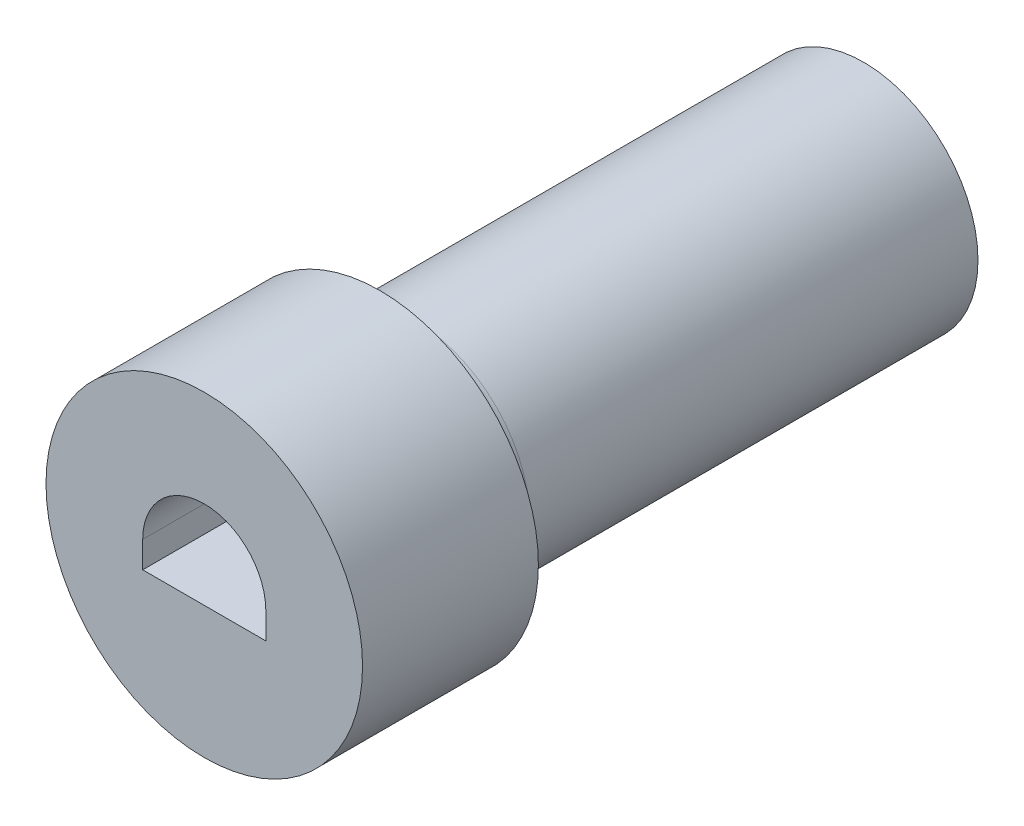
SolidWorks part; units mm, degrees
ref_plane "Front Plane" through (0, 0, 0) normal (0, 0, 1) x (1, 0, 0)
ref_plane "Top Plane" through (0, 0, 0) normal (0, 1, 0) x (1, 0, 0)
ref_plane "Right Plane" through (0, 0, 0) normal (1, 0, 0) x (0, 0, -1)
sketch "Sketch1" plane through (0, 0, 0) normal (0, 0, 1) x (1, 0, 0)
  circle A0 centre (0, 0) radius 1.651
  dimension "D1" = 3.302
extrude "Boss-Extrude1" add sketch "Sketch1" along normal blind 6.985
sketch "Sketch2" plane through (0, 0, 6.985) normal (0, 0, 1) x (1, 0, 0)
  line L0 (-0.889, 0) -> (-0.889, -0.381)
  line L1 (-0.889, -0.381) -> (0.7112, -0.381)
  line L3 (0.889, 0) -> (0.889, -0.381)
  line L4 (0.889, -0.381) -> (0.7112, -0.381)
  arc A0 (0.889, 0) -> (-0.889, 0) centre (0, 0) ccw
sketch "Sketch3" plane through (0, 0, 6.985) normal (0, 0, 1) x (1, 0, 0)
  circle A0 centre (0, 0) radius 2.286
  dimension "D1" = 4.572
extrude "Boss-Extrude2" add sketch "Sketch3" along normal blind 2.54
extrude "Cut-Extrude3" cut sketch "Sketch2" along normal blind 2.54 and the other way blind 2.54
fillet "Fillet1" radius 0.508 1 edges at (1.651, 0, 6.985)
